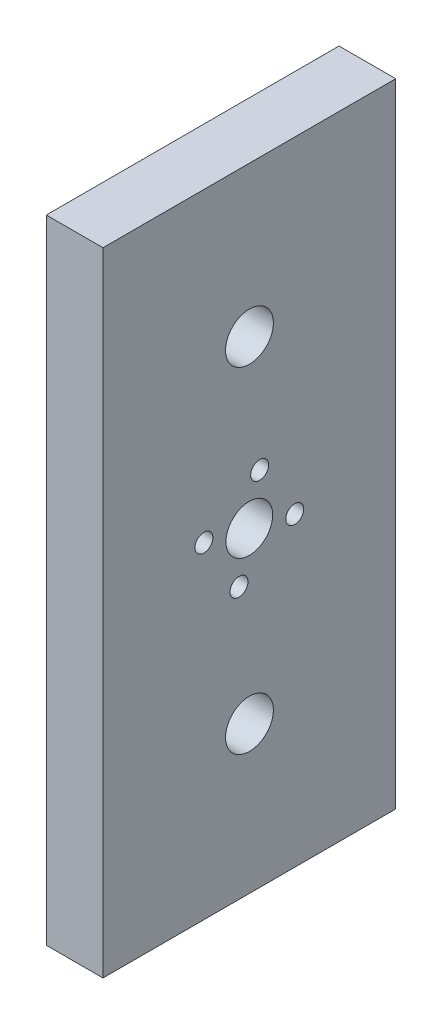
SolidWorks part; units mm, degrees
ref_plane "Front Plane" through (0, 0, 0) normal (0, 0, 1) x (1, 0, 0)
ref_plane "Top Plane" through (0, 0, 0) normal (0, 1, 0) x (1, 0, 0)
ref_plane "Right Plane" through (0, 0, 0) normal (1, 0, 0) x (0, 0, -1)
sketch "Sketch2" plane through (0, 0, 0) normal (1, 0, 0) x (0, 0, -1)
  line L1 (391.1257, -434.0649) -> (442.7965, -434.0649)
  line L2 (391.1257, -434.0649) -> (391.1257, -545.6949)
  line L3 (391.1257, -545.6949) -> (442.7965, -545.6949)
  line L4 (442.7965, -434.0649) -> (442.7965, -545.6949)
  line L5 (391.1257, -434.0649) -> (442.7965, -545.6949) construction
  line L6 (391.1257, -545.6949) -> (442.7965, -434.0649) construction
  point P0 (416.9611, -489.8799)
extrude "Boss-Extrude1" add sketch "Sketch2" along normal blind 10
sketch "Sketch3" plane through (10, 0, 0) normal (1, 0, 0) x (0, 0, -1)
  circle A0 centre (416.9826, -460.5787) radius 4.225
  circle A1 centre (416.9826, -519.7607) radius 4.225
  circle A2 centre (416.9611, -489.8799) radius 4.1275
  dimension "D1" = 8.45
  dimension "D2" = 8.45
  dimension "D3" = 8.255
extrude "Cut-Extrude1" cut sketch "Sketch3" against normal through all
sketch "Sketch5" plane through (10, 0, 0) normal (1, 0, 0) x (0, 0, -1)
  circle A0 centre (418.7857, -481.8598) radius 1.5875
  circle A1 centre (424.9811, -491.7045) radius 1.5875
  circle A2 centre (415.1364, -497.8999) radius 1.5875
  circle A3 centre (408.941, -488.0552) radius 1.5875
  dimension "D1" = 3.175
extrude "Cut-Extrude2" cut sketch "Sketch5" against normal through all
